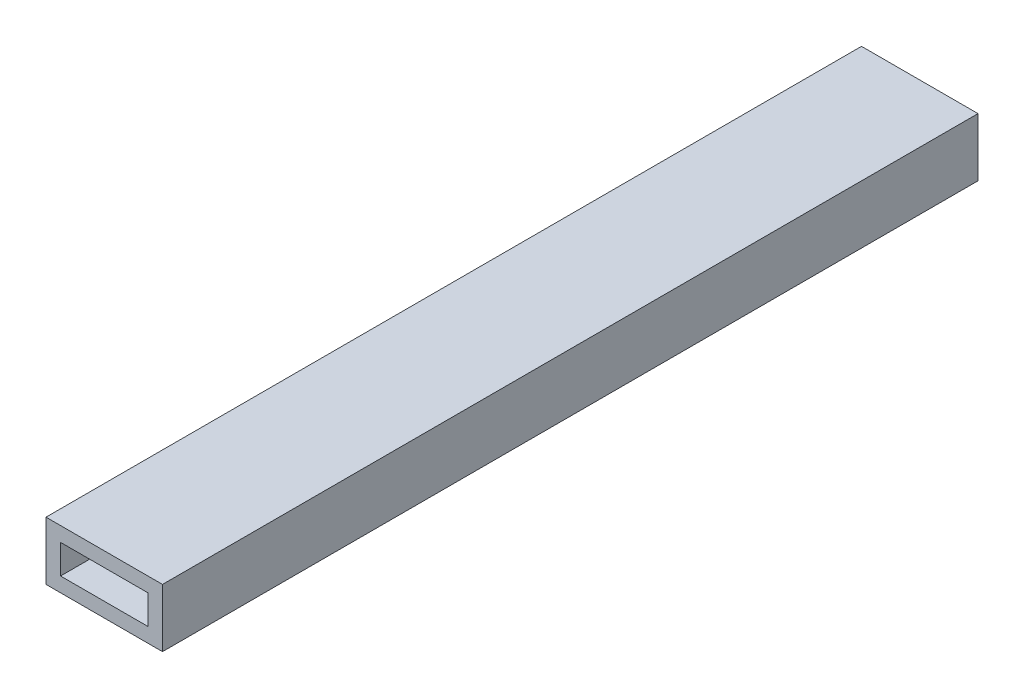
SolidWorks part; units mm, degrees
material "6063-T6"
ref_plane "Front" through (0, 0, 0) normal (0, 0, 1) x (1, 0, 0)
ref_plane "Top" through (0, 0, 0) normal (0, 1, 0) x (1, 0, 0)
ref_plane "Right" through (0, 0, 0) normal (1, 0, 0) x (0, 0, -1)
sketch "Sketch1" plane through (0, 0, 0) normal (0, 0, 1) x (1, 0, 0)
  line L0 (3.175, 9.525) -> (22.225, 9.525)
  line L1 (0, 0) -> (25.4, 0)
  line L2 (0, 0) -> (0, 12.7)
  line L3 (0, 12.7) -> (25.4, 12.7)
  line L4 (25.4, 0) -> (25.4, 12.7)
  line L5 (0, 0) -> (25.4, 12.7) construction
  line L6 (0, 12.7) -> (25.4, 0) construction
  line L7 (22.225, 3.175) -> (22.225, 9.525)
  line L8 (3.175, 3.175) -> (22.225, 3.175)
  line L9 (3.175, 3.175) -> (3.175, 9.525)
  point P4 (12.7, 6.35)
  dimension "D1" = 12.7
  dimension "D2" = 25.4
  dimension "D3" = 3.175
extrude "Boss-Extrude1" add sketch "Sketch1" along normal blind 177.8
